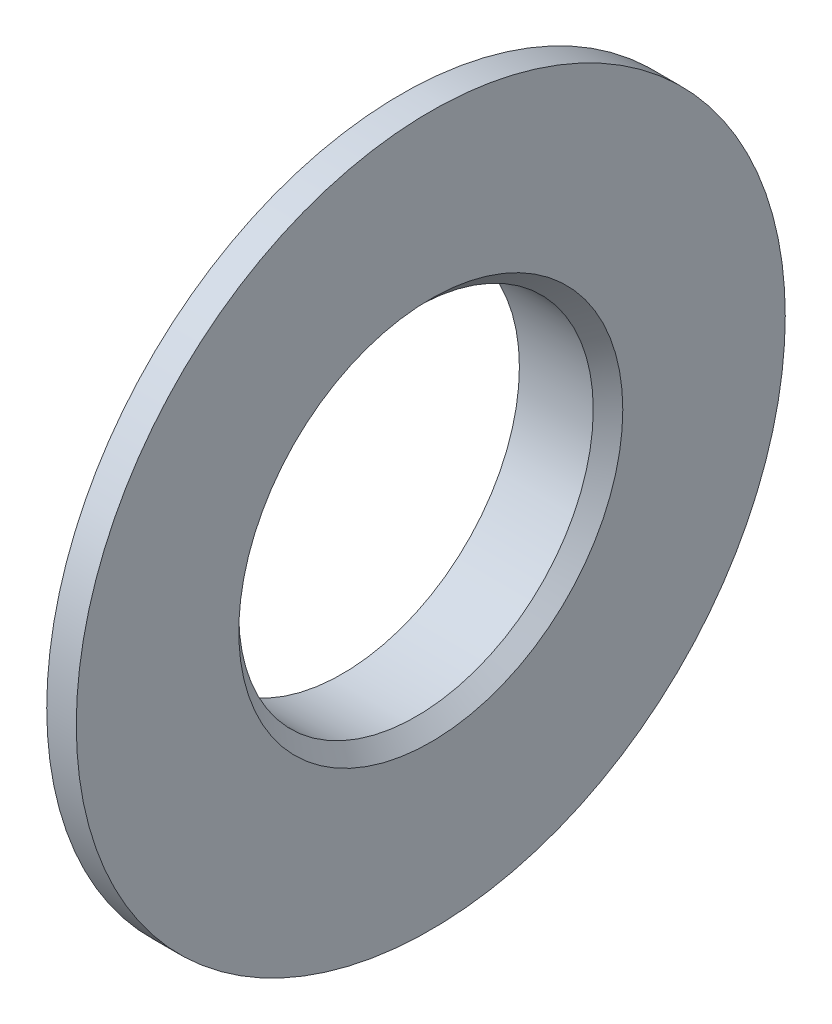
SolidWorks part; units mm, degrees
material "Alloy Steel (SS)"
ref_plane "Front Plane" through (0, 0, 0) normal (0, 0, 1) x (1, 0, 0)
ref_plane "Top Plane" through (0, 0, 0) normal (0, 1, 0) x (1, 0, 0)
ref_plane "Right Plane" through (0, 0, 0) normal (1, 0, 0) x (0, 0, -1)
sketch "Sketch1" plane through (0, 0, 0) normal (0, 0, 1) x (1, 0, 0)
  line L0 (0, 0) -> (0, 6) construction
  line L1 (0, 6) -> (-1, 6)
  line L4 (-1, 7) -> (-1, 12)
  line L5 (-1, 12) -> (0, 12)
  line L6 (0, 12) -> (0, 6)
  line L7 (0, 0) -> (-10.5933, 0) construction
  line L9 (-1, 6) -> (-3, 6)
  line L10 (-3, 6) -> (-3, 7)
  line L11 (-3, 7) -> (-1, 7)
  dimension "D1" = 6
  dimension "D2" = 6
  dimension "D3" = 1
  dimension "D4" = 3
  dimension "D5" = 1
revolve "Revolve1" add sketch "Sketch1" angle 360 about L7
chamfer "Chamfer1" distance 0.5 angle 45 1 edges at (0, 0, -6)
